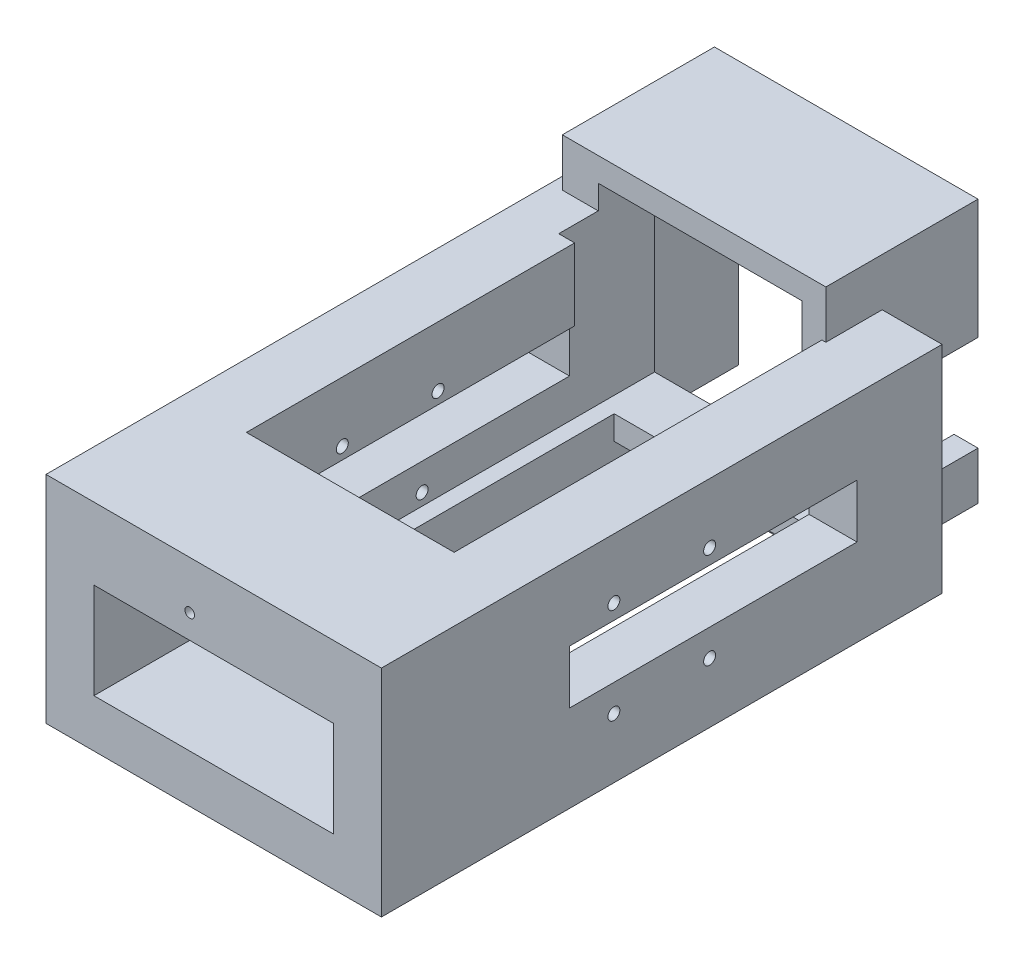
SolidWorks part; units mm, degrees
ref_plane "Alzado" through (0, 0, 0) normal (0, 0, 1) x (1, 0, 0)
ref_plane "Planta" through (0, 0, 0) normal (0, 1, 0) x (1, 0, 0)
ref_plane "Vista lateral" through (0, 0, 0) normal (1, 0, 0) x (0, 0, -1)
sketch "Croquis1" plane through (0, 0, 0) normal (0, 1, 0) x (1, 0, 0)
  line L1 (-35, -58.5) -> (35, -58.5)
  line L2 (-35, -58.5) -> (-35, 58.5)
  line L3 (-35, 58.5) -> (35, 58.5)
  line L4 (35, -58.5) -> (35, 58.5)
  line L5 (-35, -58.5) -> (35, 58.5) construction
  line L6 (-35, 58.5) -> (35, -58.5) construction
  point P0 (0, 0)
  dimension "D1" = 117
  dimension "D2" = 70
extrude "Saliente-Extruir1" add sketch "Croquis1" along normal blind 5 contours L3 L4 L1 L2
sketch "Croquis2" plane through (0, 5, 0) normal (0, 1, 0) x (1, 0, 0)
  line L0 (-35, 58.5) -> (-35, 46.75)
  line L1 (-35, -58.5) -> (-35, 58.5) construction
  line L2 (-35, 46.75) -> (35, 46.75)
  line L3 (35, -58.5) -> (35, 58.5) construction
  line L4 (35, 46.75) -> (35, 58.5)
  line L5 (35, 58.5) -> (-35, 58.5)
  line L6 (-35, -58.5) -> (-35, -46.75)
  line L7 (-35, -46.75) -> (35, -46.75)
  line L8 (35, -46.75) -> (35, -58.5)
  line L9 (35, -58.5) -> (-35, -58.5)
  dimension "D1" = 11.75
extrude "Saliente-Extruir2" add sketch "Croquis2" along normal blind 40
sketch "Croquis5" plane through (0, 0, -58.5) normal (0, 0, -1) x (-1, 0, 0)
  line L1 (-35, 45) -> (35, 45)
  line L2 (-35, 45) -> (-35, 5)
  line L3 (-35, 5) -> (35, 5)
  line L4 (35, 45) -> (35, 5)
  circle A0 centre (5, 35) radius 1
  dimension "D2" = 2
  dimension "D1" = 10
  dimension "D3" = 40
extrude "Cortar-Extruir3" cut sketch "Croquis5" against normal through all contours A0
sketch "Croquis3" plane through (0, 5, 0) normal (0, 1, 0) x (1, 0, 0)
  line L0 (21.675, 51.55) -> (-21.675, 51.55)
  line L2 (-21.675, 51.55) -> (-21.675, -30)
  line L3 (-21.675, -30) -> (21.675, -30)
  line L4 (21.675, -30) -> (21.675, 51.55)
  line L5 (-24.75, 0) -> (24.75, 0) construction
  line L7 (0, -24.75) -> (0, 24.75) construction
  dimension "D1" = 81.55
  dimension "D2" = 30
  dimension "D3" = 43.35
  dimension "D4" = 21.675
extrude "Cortar-Extruir1" cut sketch "Croquis3" against normal blind 10
sketch "Croquis7" plane through (-35, 0, 0) normal (-1, 0, 0) x (0, 0, 1)
  line L1 (38.5, 0) -> (-38.5, 0) construction
  line L2 (-58.5, 45) -> (-58.5, 0) construction
  line L3 (-40.75, 29.3408) -> (19.25, 29.3408)
  line L4 (-40.75, 29.3408) -> (-40.75, 18.1498)
  line L5 (-40.75, 18.1498) -> (19.25, 18.1498)
  line L6 (19.25, 29.3408) -> (19.25, 18.1498)
  line L8 (0, -24.75) -> (0, 24.75) construction
  circle A0 centre (-9.99, 32.49) radius 1.25
  circle A1 centre (9.99, 32.49) radius 1.25
  circle A2 centre (9.99, 12.51) radius 1.25
  circle A3 centre (-9.99, 12.51) radius 1.25
  dimension "D4" = 2.5
  dimension "D1" = 19.98
  dimension "D2" = 12.51
  dimension "D3" = 19.98
  dimension "D5" = 17.75
  dimension "D6" = 9.99
  dimension "D7" = 9.26
sketch "Croquis8" plane through (0, 5, 0) normal (0, 1, 0) x (1, 0, 0)
  line L1 (-35, 46.75) -> (35, 46.75)
  line L2 (-35, 46.75) -> (-35, -46.75)
  line L3 (-35, -46.75) -> (35, -46.75)
  line L4 (35, 46.75) -> (35, -46.75)
  line L5 (-21.675, 46.75) -> (21.675, 46.75)
  line L6 (-21.675, 46.75) -> (-21.675, -30)
  line L7 (-21.675, -30) -> (21.675, -30)
  line L8 (21.675, 46.75) -> (21.675, -30)
  line M1 (35, 46.75) -> (21.675, 46.75)
  line M2 (21.675, 46.75) -> (21.675, -30)
  line M3 (21.675, -30) -> (-21.675, -30)
  line M4 (-21.675, -30) -> (-21.675, 46.75)
  line M5 (-21.675, 46.75) -> (-35, 46.75)
  line M6 (-35, 46.75) -> (-35, -46.75)
  line M7 (-35, -46.75) -> (35, -46.75)
  line M8 (35, -46.75) -> (35, 46.75)
extrude "Saliente-Extruir4" add sketch "Croquis8" along normal blind 40 contours M8 M1 M2 M3 M4 M5 M6 M7
extrude "Cortar-Extruir5" cut sketch "Croquis7" against normal through all
sketch "Croquis9" plane through (0, 0, 58.5) normal (0, 0, 1) x (1, 0, 0)
  line L0 (0, -30.25) -> (0, 30.25) construction
  line L1 (-25, 30) -> (25, 30)
  line L2 (-25, 30) -> (-25, 10)
  line L3 (-25, 10) -> (25, 10)
  line L4 (25, 30) -> (25, 10)
  line L5 (-35, 0) -> (35, 0) construction
  dimension "D1" = 25
  dimension "D2" = 50
  dimension "D3" = 20
  dimension "D4" = 10
extrude "Cortar-Extruir6" cut sketch "Croquis9" against normal through all contours L1 L4 L3 L2
sketch "Croquis11" plane through (0, 0, -58.5) normal (0, 0, -1) x (-1, 0, 0)
  line L0 (-35, 45) -> (35, 45) construction
  line L1 (-17.5, 45) -> (27.5, 45)
  line L2 (-17.5, 45) -> (-17.5, 0)
  line L3 (-17.5, 0) -> (27.5, 0)
  line L4 (27.5, 45) -> (27.5, 0)
  line L5 (38.5, 0) -> (-38.5, 0) construction
  line L7 (-22.5, 45) -> (32.5, 45)
  line L8 (-22.5, 45) -> (-22.5, 0)
  line L9 (-22.5, 0) -> (32.5, 0)
  line L10 (32.5, 45) -> (32.5, 0)
  circle A0 centre (5, 35) radius 1 construction
  line M10 (25, 10) -> (-25, 10)
  line M12 (-25, 30) -> (25, 30)
  line M14 (-35, 0) -> (35, 0)
  line M16 (35, 45) -> (-35, 45)
  dimension "D2" = 22.5
  dimension "D3" = 22.5
  dimension "D1" = 5
  dimension "D4" = 5
extrude "Saliente-Extruir5" add sketch "Croquis11" along normal blind 20 contours L10 L4 M16 M14 | L8 L2 M16 M12 | L8 L2 M10 M14
sketch "Croquis12" plane through (0, 0, -58.5) normal (0, 0, -1) x (-1, 0, 0)
  line L0 (-17.5, 45) -> (-17.5, 30) construction
  line L1 (-17.5, 45) -> (25, 45)
  line L2 (-17.5, 45) -> (-17.5, 30)
  line L3 (-17.5, 30) -> (25, 30)
  line L4 (25, 45) -> (25, 30)
  line L5 (-17.5, 45) -> (27.5, 45) construction
  dimension "D1" = 0
extrude "Cortar-Extruir7" cut sketch "Croquis12" against normal blind 20 contours L1 L4 L3 L2
sketch "Croquis13" plane through (0, 45, 0) normal (0, 1, 0) x (1, 0, 0)
  line L1 (-32.5, 78.5) -> (-27.5, 78.5)
  line L2 (-32.5, 78.5) -> (-32.5, 46.75)
  line L3 (-32.5, 46.75) -> (-25, 46.75)
  line L6 (-27.5, 78.5) -> (-27.5, 58.5)
  line L7 (-27.5, 58.5) -> (-25, 58.5)
  line L10 (-25, 58.5) -> (-25, 46.75)
  line L19 (17.5, 78.5) -> (22.5, 78.5)
  line L20 (17.5, 78.5) -> (17.5, 46.75)
  line L21 (17.5, 46.75) -> (22.5, 46.75)
  line L22 (22.5, 78.5) -> (22.5, 46.75)
extrude "Saliente-Extruir6" add sketch "Croquis13" along normal blind 5
sketch "Croquis14" plane through (0, 50, 0) normal (0, 1, 0) x (1, 0, 0)
  line L1 (-32.5, 78.5) -> (22.5, 78.5)
  line L2 (-32.5, 78.5) -> (-32.5, 46.75)
  line L3 (-32.5, 46.75) -> (22.5, 46.75)
  line L4 (22.5, 78.5) -> (22.5, 46.75)
extrude "Saliente-Extruir7" add sketch "Croquis14" along normal blind 5
